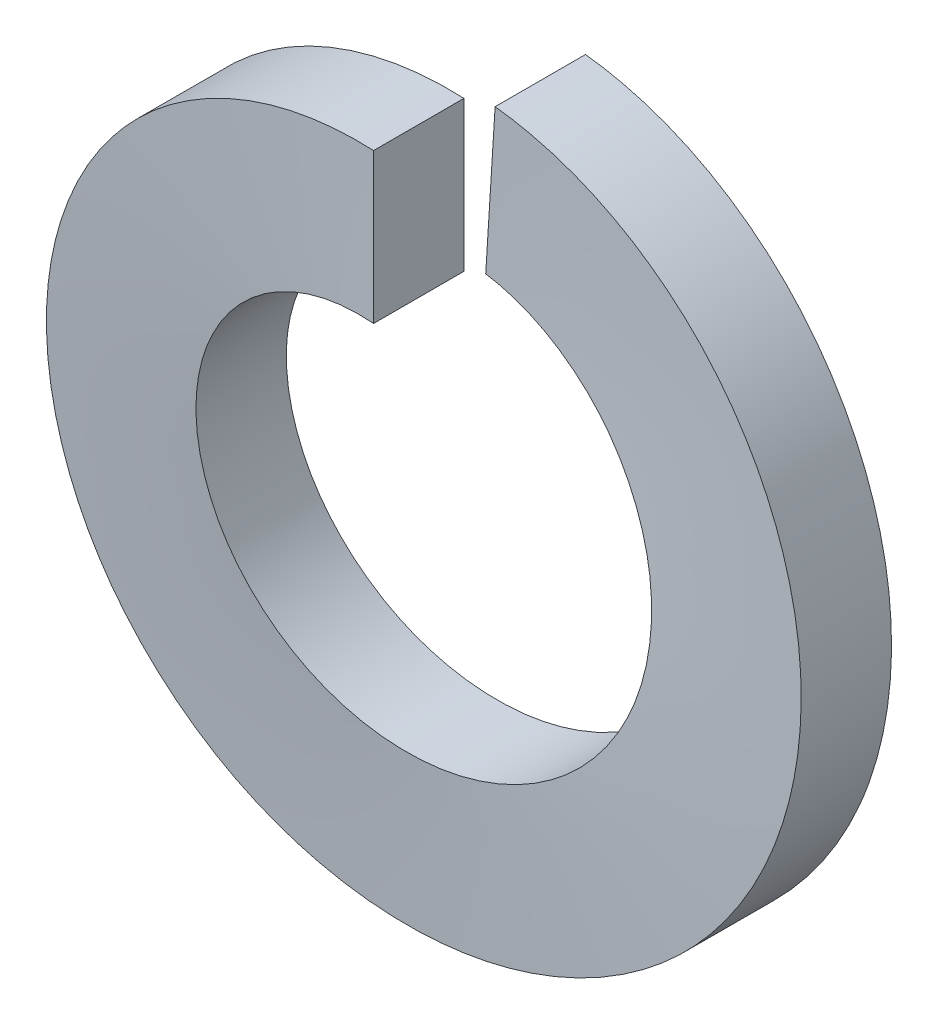
SolidWorks part; units mm, degrees
ref_plane "Front Plane" through (0, 0, 0) normal (0, 0, 1) x (1, 0, 0)
ref_plane "Top Plane" through (0, 0, 0) normal (0, 1, 0) x (1, 0, 0)
ref_plane "Right Plane" through (0, 0, 0) normal (1, 0, 0) x (0, 0, -1)
sketch "Sketch1" plane through (0, 0, 0) normal (0, 0, 1) x (1, 0, 0)
  line L0 (0, 7.4) -> (0, 4.25) construction
  circle A0 centre (0, 0) radius 7.4
  circle A1 centre (0, 0) radius 4.25 construction
  dimension "ID" = 8.5
  dimension "OD" = 14.8
curve "Helix/Spiral1" pitch 2.1111 height 2.09 turns 0.99 parameters "HT"=2.09
sketch "Sketch2" plane through (0, 0, 0) normal (1, 0, 0) x (0, 0, -1)
  line L1 (0, 7.4) -> (-1.9, 7.4)
  line L2 (0, 7.4) -> (0, 4.25)
  line L3 (0, 4.25) -> (-1.9, 4.25)
  line L4 (-1.9, 7.4) -> (-1.9, 4.25)
  dimension "THK" = 1.9
sweep "Sweep1" add profiles "Sketch2" path "Helix/Spiral1"
equation "\"HT@Helix/Spiral1\" = \"THK@Sketch2\"*1.1"
